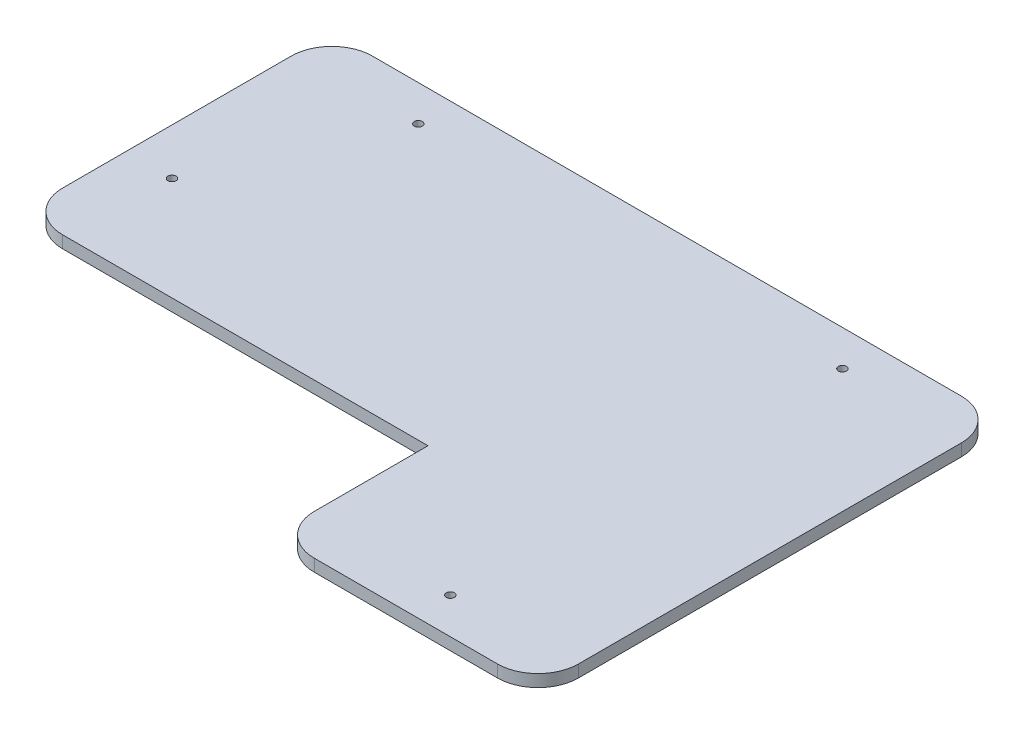
SolidWorks part; units mm, degrees
ref_plane "Front Plane" through (0, 0, 0) normal (0, 0, 1) x (1, 0, 0)
ref_plane "Top Plane" through (0, 0, 0) normal (0, 1, 0) x (1, 0, 0)
ref_plane "Right Plane" through (0, 0, 0) normal (1, 0, 0) x (0, 0, -1)
sketch "Sketch1" plane through (0, 0, 0) normal (0, 1, 0) x (1, 0, 0)
  line L1 (82.55, 57.15) -> (-82.55, 57.15)
  line L2 (82.55, 57.15) -> (82.55, -57.15)
  line L3 (82.55, -57.15) -> (-82.55, -57.15)
  line L4 (-82.55, 57.15) -> (-82.55, -57.15)
  line L5 (82.55, 57.15) -> (-82.55, -57.15) construction
  line L6 (82.55, -57.15) -> (-82.55, 57.15) construction
  point P0 (0, 0)
  dimension "D1" = 114.3
  dimension "D2" = 165.1
extrude "Boss-Extrude1" add sketch "Sketch1" along normal blind 3
fillet "Fillet1" [suppressed] radius 10
sketch "Sketch2" plane through (0, 3, 0) normal (0, 1, 0) x (1, 0, 0)
  line L1 (-82.55, -57.15) -> (17.45, -57.15)
  line L2 (-82.55, -57.15) -> (-82.55, -19.15)
  line L3 (-82.55, -19.15) -> (17.45, -19.15)
  line L4 (17.45, -57.15) -> (17.45, -19.15)
  dimension "D1" = 100
  dimension "D2" = 38
extrude "Cut-Extrude1" cut sketch "Sketch2" against normal through all
fillet "Fillet2" radius 10 5 edges at (17.45, 1.5, 57.15) (-82.55, 1.5, 19.15) (82.55, 1.5, -57.15) (82.55, 1.5, 57.15) (-82.55, 1.5, -57.15)
sketch "Sketch3" plane through (0, 3, 0) normal (0, 1, 0) x (1, 0, 0)
  circle A0 centre (52.07, -48.26) radius 1.5 construction
  circle A1 centre (-71.12, 6.35) radius 1.5 construction
  circle A2 centre (52.07, 48.34) radius 1.5 construction
  circle A3 centre (-52.43, 48.34) radius 1.5 construction
  circle A4 centre (52.07, -48.26) radius 1.5
  circle A5 centre (-71.12, 6.35) radius 1.5
  circle A6 centre (52.07, 48.34) radius 1.5
  circle A7 centre (-52.43, 48.34) radius 1.5
  circle A8 centre (-52.43, 48.34) radius 1
  circle A9 centre (-71.12, 6.35) radius 1
  circle A10 centre (52.07, -48.26) radius 1
  circle A11 centre (52.07, 48.34) radius 1
  dimension "D1" = 0.5
extrude "Cut-Extrude3" cut sketch "Sketch3" against normal through all contours A8 | A9 | A11 | A10
